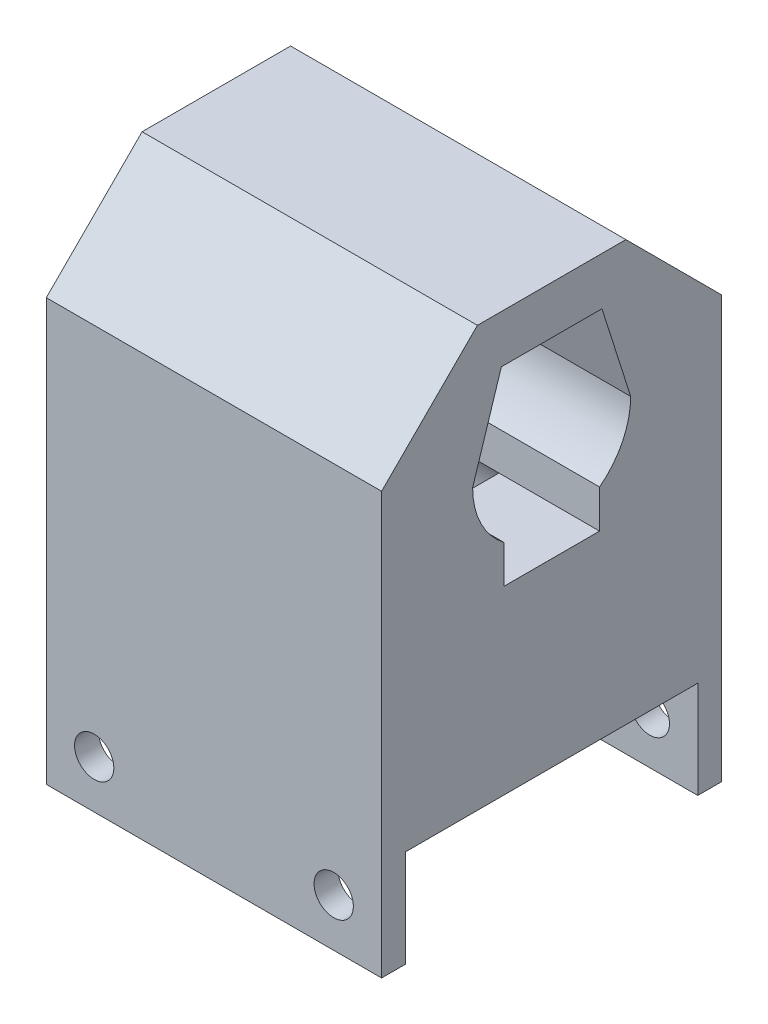
SolidWorks part; units mm, degrees
ref_plane "前视基准面" through (0, 0, 0) normal (0, 0, 1) x (1, 0, 0)
ref_plane "上视基准面" through (0, 0, 0) normal (0, 1, 0) x (1, 0, 0)
ref_plane "右视基准面" through (0, 0, 0) normal (1, 0, 0) x (0, 0, -1)
other "Configuration Table"
sketch "Sketch1" plane through (0, 0, 0) normal (1, 0, 0) x (0, 0, -1)
  line L0 (0, 0) -> (30.5, 0) construction
  line L1 (0, 0) -> (-30.5, 0) construction
  line L2 (-30.5, 0) -> (-30.5, 20)
  line L3 (-30.5, 20) -> (-30.5, 98)
  line L4 (-30.5, 98) -> (30.5, 98)
  line L5 (30.5, 98) -> (30.5, 0)
  line L6 (-30.5, 0) -> (-35.5, 0)
  line L7 (-35.5, 0) -> (-35.5, 108)
  line L8 (0, 0) -> (0, 20) construction
  line L9 (30.5, 0) -> (35.5, 0)
  line L10 (35.5, 0) -> (35.5, 108)
  line L11 (-35.5, 108) -> (35.5, 108)
  dimension "D2" = 30.5
  dimension "D3" = 20
extrude "Boss-Extrude1" add sketch "Sketch1" against normal blind 70
sketch "Sketch3" plane through (0, 0, 0) normal (0, 0, 1) x (1, 0, 0)
  line L0 (-70, 0) -> (-70, 20) construction
  line L1 (-70, 108) -> (-70, 0) construction
  line L2 (-70, 20) -> (0, 20) construction
  line L3 (0, -55) -> (0, 55) construction
  line L4 (0, 20) -> (0, 0) construction
  line L5 (0, 0) -> (-70, 0) construction
  line L6 (-70, 10) -> (-60, 10) construction
  line L7 (0, 10) -> (-10, 10) construction
  circle A0 centre (-60, 10) radius 4.1
  circle A1 centre (-10, 10) radius 4.1
extrude "Cut-Extrude2" cut sketch "Sketch3" against normal through all both and the other way through all
sketch "Sketch4" plane through (0, 0, 0) normal (1, 0, 0) x (0, 0, -1)
  line L0 (-30.5, 98) -> (-10.5, 98)
  line L1 (-30.5, 98) -> (30.5, 98) construction
  line L2 (-30.5, 98) -> (-30.5, 79.151)
  line L3 (-10.5, 98) -> (-16.5, 79.151)
  line L5 (0, 108) -> (0, 98) construction
  line L6 (35.5, 108) -> (-35.5, 108) construction
  line L7 (0, 79.151) -> (-30.5, 79.151) construction
  line L10 (-30.5, 79.151) -> (-16.5, 79.151)
  line L15 (30.5, 0) -> (35.5, 0)
  line L16 (35.5, 0) -> (35.5, 108)
  line L17 (35.5, 108) -> (-35.5, 108)
  line L18 (-35.5, 108) -> (-35.5, 0)
  line L19 (-35.5, 0) -> (-30.5, 0)
  line L20 (-30.5, 0) -> (-30.5, 98)
  line L21 (-30.5, 98) -> (30.5, 98)
  line L22 (30.5, 98) -> (30.5, 0)
  line L29 (-30.5, 98) -> (-10.5, 98) construction
  circle A0 centre (0, 79.151) radius 15 construction
  dimension "D1" = 20
  dimension "D2" = 18.849
  dimension "D4" = 14
  dimension "D3" = 0
extrude "Boss-Extrude2" add sketch "Sketch4" against normal blind 70
mirror "Mirror2" about plane through (0, 0, 0) normal (0, 0, 1) of "Boss-Extrude2"
sketch "Sketch5" plane through (-70, 0, 0) normal (-1, 0, 0) x (0, 0, 1)
  line L1 (-30.5, 79.151) -> (-30.5, 0) construction
  line L2 (-30.5, 62.151) -> (-30.5, 79.151)
  line L3 (-30.5, 79.151) -> (-16.5, 79.151)
  line L4 (0, 79.151) -> (0, 63.651) construction
  line L9 (-10, 62.151) -> (-10, 66.0266)
  line L10 (-30.5, 41.305) -> (-30.5, 62.151)
  line L11 (-10, 62.151) -> (-10, 58.0457)
  line L12 (-30.5, 41.305) -> (-30.5, 20.305)
  line L13 (-9.5122, 24.2824) -> (-9.5122, 20.305)
  line L15 (-9.5122, 20.305) -> (-30.5, 20.305)
  arc A3 (-10, 58.0457) -> (-19.5, 41.305) centre (0, 41.305) ccw construction
  arc A4 (-10, 58.0457) -> (-9.5122, 24.2824) centre (0, 41.305) ccw
  arc A5 (-16.5, 79.151) -> (-10, 66.0266) centre (0, 79.151) ccw
  point P2 (0, 0)
  dimension "D1" = 20.5
  dimension "D2" = 19.5
extrude "Boss-Extrude5" add sketch "Sketch5" against normal blind 70
mirror "Mirror3" about plane through (0, 0, 0) normal (0, 0, 1) of "Boss-Extrude5"
sketch "Sketch6" plane through (0, 0, 0) normal (1, 0, 0) x (0, 0, -1)
  line L1 (-9.5122, 20.305) -> (9.5122, 20.305)
  line L2 (9.5122, 20.305) -> (9.5122, 24.2824)
  line L3 (-9.5122, 20.305) -> (-9.5122, 24.2824)
  line L4 (-10, 58.0457) -> (10, 58.0457)
  arc A0 (9.5122, 24.2824) -> (10, 58.0457) centre (0, 41.305) ccw
  arc A1 (-10, 58.0457) -> (-9.5122, 24.2824) centre (0, 41.305) ccw
extrude "Boss-Extrude6" add sketch "Sketch6" against normal blind 21
mirror "Mirror1" about plane through (0, 0, 0) normal (0, 0, 1) of "Boss-Extrude2"
chamfer "Chamfer1" distance 20 angle 45 2 edges at (-35, 108, -35.5) (-35, 108, 35.5)
chamfer "Chamfer4" distance 1 angle 45 9 edges at (-70, 41.0233, -19.498) (-70, 41.0233, 19.498) (-70, 71.8281, -14.786) (-70, 71.8281, 14.786) (-70, 88.5755, 13.5) (-70, 88.5755, -13.5) (-70, 98, 0) (-70, 62.0361, -10) (-70, 62.0361, 10)
